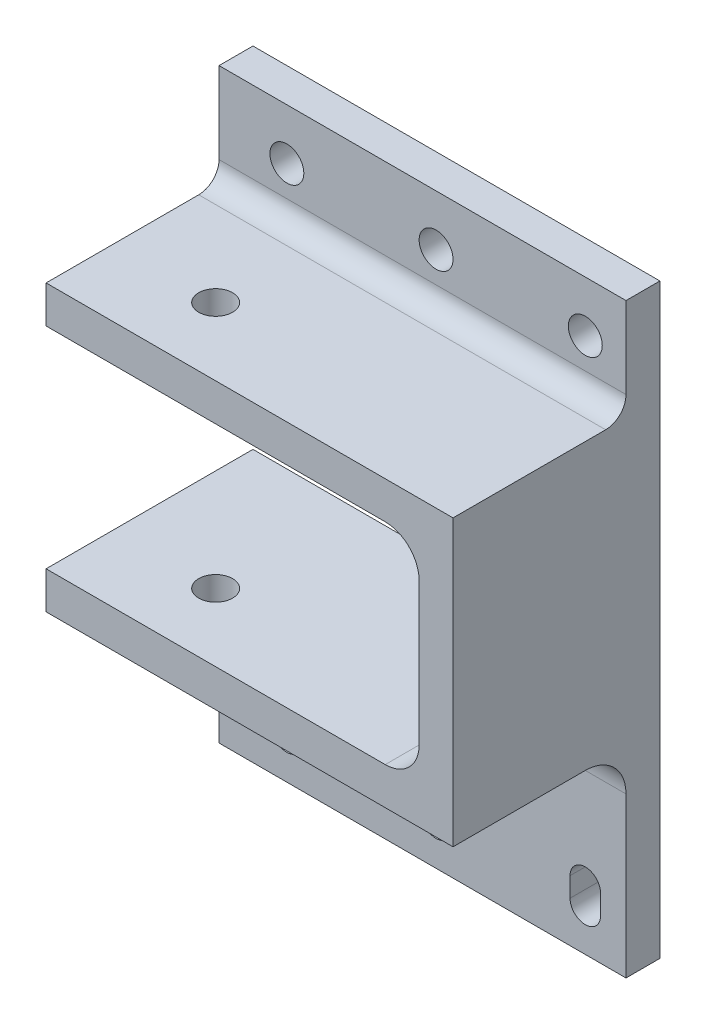
SolidWorks part; units mm, degrees
ref_plane "Front Plane" through (0, 0, 0) normal (0, 0, 1) x (1, 0, 0)
ref_plane "Top Plane" through (0, 0, 0) normal (0, 1, 0) x (1, 0, 0)
ref_plane "Right Plane" through (0, 0, 0) normal (1, 0, 0) x (0, 0, -1)
sketch "Sketch2" plane through (0, 0, 0) normal (0, 1, 0) x (1, 0, 0)
  line L1 (32.5, -25) -> (-32.5, -25)
  line L2 (32.5, -25) -> (32.5, 25)
  line L3 (32.5, 25) -> (-32.5, 25)
  line L4 (-32.5, -25) -> (-32.5, 25)
  line L5 (32.5, -25) -> (-32.5, 25) construction
  line L6 (32.5, 25) -> (-32.5, -25) construction
  point P0 (0, 0)
  dimension "D1" = 65
  dimension "D2" = 50
extrude "5" add sketch "Sketch2" along normal blind 42
sketch "Sketch3" plane through (0, 0, 25) normal (0, 0, 1) x (1, 0, 0)
  line L0 (-32.5, 42) -> (-32.5, 0) construction
  line L1 (22.5, 5.5) -> (-87.5, 5.5)
  line L2 (22.5, 5.5) -> (22.5, 36.5)
  line L3 (22.5, 36.5) -> (-87.5, 36.5)
  line L4 (-87.5, 5.5) -> (-87.5, 36.5)
  line L5 (22.5, 5.5) -> (-87.5, 36.5) construction
  line L6 (22.5, 36.5) -> (-87.5, 5.5) construction
  point P0 (-32.5, 21)
  dimension "D1" = 31
  dimension "D2" = 110
extrude "Cut-Extrude1" cut sketch "Sketch3" against normal blind 50
sketch "Sketch4" plane through (0, 42, 0) normal (0, 1, 0) x (1, 0, 0)
  line L0 (-32.5, 25) -> (-32.5, -25) construction
  circle A0 centre (-17.5, 0) radius 2.5
  dimension "D1" = 15
extrude "Cut-Extrude2" cut sketch "Sketch4" against normal blind 50
sketch "Sketch5" plane through (0, 42, 0) normal (0, 1, 0) x (1, 0, 0)
  line L0 (32.5, -25) -> (32.5, 25) construction
  line L1 (-32.5, -25) -> (32.5, -25)
  line L2 (-32.5, -25) -> (-32.5, -10)
  line L3 (-32.5, -10) -> (32.5, -10)
  line L4 (32.5, -25) -> (32.5, -10)
  dimension "D1" = 15
extrude "Cut-Extrude3" cut sketch "Sketch5" against normal blind 50
sketch "Sketch6" plane through (0, 42, 0) normal (0, 1, 0) x (1, 0, 0)
  line L0 (32.5, -10) -> (32.5, 25) construction
  line L1 (-32.5, 25) -> (32.5, 25)
  line L2 (-32.5, 25) -> (-32.5, 20.5)
  line L3 (-32.5, 20.5) -> (32.5, 20.5)
  line L4 (32.5, 25) -> (32.5, 20.5)
  dimension "D1" = 4.5
extrude "Cut-Extrude4" cut sketch "Sketch6" against normal blind 50
sketch "Sketch7" plane through (0, 0, -20.5) normal (0, 0, -1) x (-1, 0, 0)
  line L0 (-32.5, 0) -> (-32.5, 42) construction
  line L1 (32.5, 5.5) -> (-32.5, 5.5)
  line L2 (32.5, 5.5) -> (32.5, -29.5)
  line L3 (32.5, -29.5) -> (-32.5, -29.5)
  line L4 (-32.5, 5.5) -> (-32.5, -29.5)
  dimension "D1" = 0
  dimension "D2" = 35
extrude "Boss-Extrude2" add sketch "Sketch7" against normal blind 5
fillet "Fillet1" radius 5 2 edges at (22.5, 5.5, -5.25) (22.5, 36.5, -5.25)
fillet "Fillet2" radius 6 1 edges at (0, 0, -15.5)
sketch "Sketch8" plane through (0, 0, -20.5) normal (0, 0, -1) x (-1, 0, 0)
  line L0 (32.5, 42) -> (-32.5, 42) construction
  line L1 (32.5, 42) -> (-32.5, 42)
  line L2 (32.5, 42) -> (32.5, 57)
  line L3 (32.5, 57) -> (-32.5, 57)
  line L4 (-32.5, 42) -> (-32.5, 57)
  line L5 (32.5, 36.5) -> (32.5, 42) construction
  line L6 (-32.5, -29.5) -> (-32.5, 42) construction
  dimension "D1" = 0
  dimension "D2" = 15
extrude "Boss-Extrude3" add sketch "Sketch8" against normal blind 5
fillet "Fillet3" radius 3 1 edges at (0, 42, -15.5)
sketch "Sketch9" plane through (0, 0, -15.5) normal (0, 0, 1) x (1, 0, 0)
  line L0 (-32.5, 45) -> (-32.5, 57) construction
  line L1 (32.5, 42) -> (-32.5, 42) construction
  circle A0 centre (-22.5, 49.5) radius 2.5
  circle A1 centre (-0.5, 49.5) radius 2.5
  circle A2 centre (21.5, 49.5) radius 2.5
  dimension "D1" = 10
  dimension "D3" = 7.5
  dimension "D2" = 3
extrude "Cut-Extrude5" cut sketch "Sketch9" against normal blind 5
sketch "Sketch10" plane through (0, 0, -15.5) normal (0, 0, 1) x (1, 0, 0)
  line L0 (-22.5, -23.44) -> (-22.5, -20.56) construction
  line L1 (-24.75, -23.44) -> (-24.75, -20.56)
  line L2 (-20.25, -23.44) -> (-20.25, -20.56)
  line L3 (-0.5, -23.44) -> (-0.5, -20.56) construction
  line L5 (-2.75, -23.44) -> (-2.75, -20.56)
  line L6 (1.75, -23.44) -> (1.75, -20.56)
  line L7 (21.5, -23.44) -> (21.5, -20.56) construction
  line L8 (19.25, -23.44) -> (19.25, -20.56)
  line L9 (23.75, -23.44) -> (23.75, -20.56)
  line L10 (-32.5, -29.5) -> (-32.5, -6) construction
  line L11 (32.5, -29.5) -> (-32.5, -29.5) construction
  arc A0 (-24.75, -23.44) -> (-20.25, -23.44) centre (-22.5, -23.44) ccw
  arc A1 (-20.25, -20.56) -> (-24.75, -20.56) centre (-22.5, -20.56) ccw
  arc A2 (-2.75, -23.44) -> (1.75, -23.44) centre (-0.5, -23.44) ccw
  arc A3 (1.75, -20.56) -> (-2.75, -20.56) centre (-0.5, -20.56) ccw
  arc A4 (19.25, -23.44) -> (23.75, -23.44) centre (21.5, -23.44) ccw
  arc A5 (23.75, -20.56) -> (19.25, -20.56) centre (21.5, -20.56) ccw
  point P3 (-22.5, -22)
  point P12 (-0.5, -22)
  point P19 (21.5, -22)
  dimension "D1" = 7.5
  dimension "D3" = 4.5
  dimension "D4" = 10
  dimension "D2" = 3
extrude "Cut-Extrude6" cut sketch "Sketch10" against normal blind 5
sketch "Sketch11" plane through (0, 0, 10) normal (0, 0, 1) x (1, 0, 0)
  line L0 (32.5, -29.5) -> (-32.5, -29.5) construction
  line L1 (32.5, 57) -> (27.5, 57)
  line L2 (32.5, 57) -> (32.5, -29.5)
  line L3 (32.5, -29.5) -> (27.5, -29.5)
  line L4 (27.5, 57) -> (27.5, -29.5)
  dimension "D1" = 5
extrude "Cut-Extrude8" cut sketch "Sketch11" against normal blind 71
